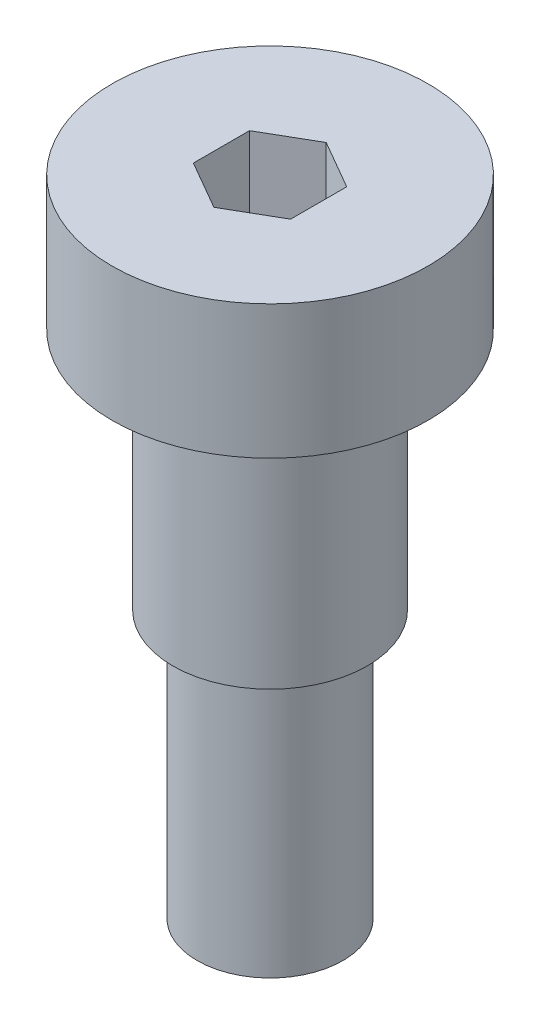
SolidWorks part; units mm, degrees
ref_plane "Front" through (0, 0, 0) normal (0, 0, 1) x (1, 0, 0)
ref_plane "Top" through (0, 0, 0) normal (0, 1, 0) x (1, 0, 0)
ref_plane "Right" through (0, 0, 0) normal (1, 0, 0) x (0, 0, -1)
sketch "profile" plane through (0, 0, 0) normal (0, 0, 1) x (1, 0, 0)
  line L0 (0, 24.8324) -> (0, -34.6109) construction
  line L1 (0, 5.5) -> (6.5, 5.5)
  line L2 (6.5, 5.5) -> (6.5, 0)
  line L3 (6.5, 0) -> (4, 0)
  line L4 (4, 0) -> (4, -10)
  line L5 (4, -10) -> (3, -10)
  line L6 (3, -10) -> (3, -21)
  line L7 (3, -21) -> (0, -21)
  line L8 (0, -21) -> (0, 5.5)
  dimension "head_diameter" = 13
  dimension "shoulder_diameter" = 8
  dimension "thread_diameter" = 6
  dimension "head_height" = 5.5
  dimension "shoulder_length" = 10
  dimension "thread_length" = 11
revolve "Base-Revolve" add sketch "profile" angle 360 about L0
sketch "socket shape" plane through (0, 5.5, 0) normal (0, 1, 0) x (-1, 0, 0)
  line L1 (0, 2.3094) -> (-2, 1.1547)
  line L2 (-2, 1.1547) -> (-2, -1.1547)
  line L3 (-2, -1.1547) -> (0, -2.3094)
  line L4 (0, -2.3094) -> (2, -1.1547)
  line L5 (2, -1.1547) -> (2, 1.1547)
  line L6 (2, 1.1547) -> (0, 2.3094)
  circle A0 centre (0, 0) radius 2 construction
  dimension "socket_width" = 4
extrude "socket" cut sketch "socket shape" against normal blind 3
